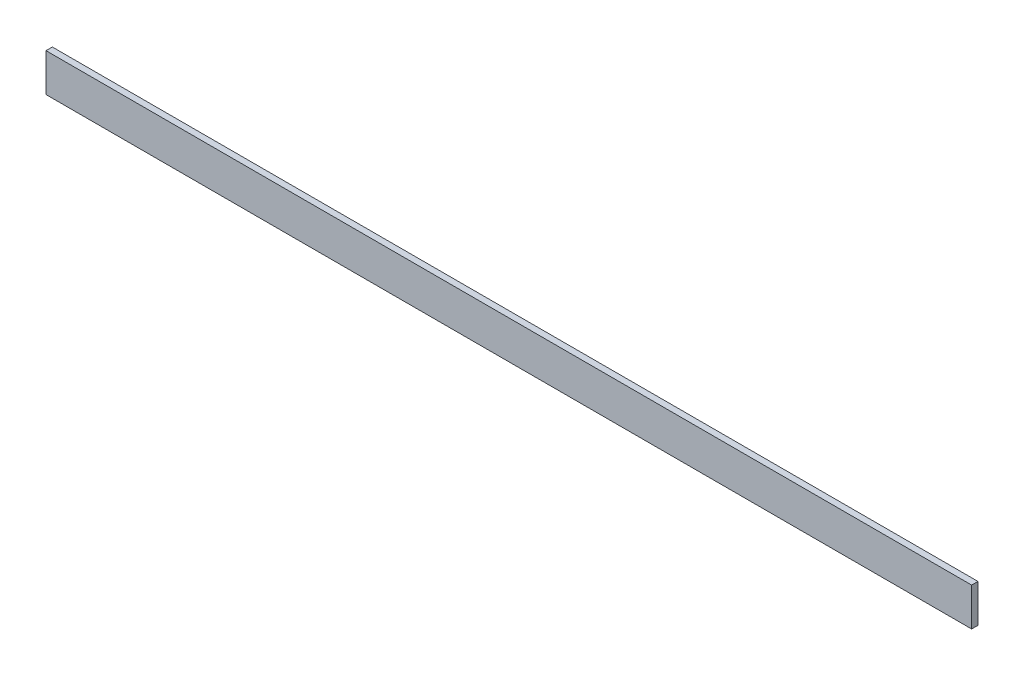
SolidWorks part; units mm, degrees
ref_plane "Спереди" through (0, 0, 0) normal (0, 0, 1) x (1, 0, 0)
ref_plane "Сверху" through (0, 0, 0) normal (0, 1, 0) x (1, 0, 0)
ref_plane "Справа" through (0, 0, 0) normal (1, 0, 0) x (0, 0, -1)
sketch "Эскиз1" plane through (0, 0, 0) normal (1, 0, 0) x (0, 0, -1)
  line L1 (0, 0) -> (5, 0)
  line L2 (0, 0) -> (0, 30)
  line L3 (0, 30) -> (5, 30)
  line L4 (5, 0) -> (5, 30)
extrude "Бобышка-Вытянуть1" add sketch "Эскиз1" along normal blind 730
